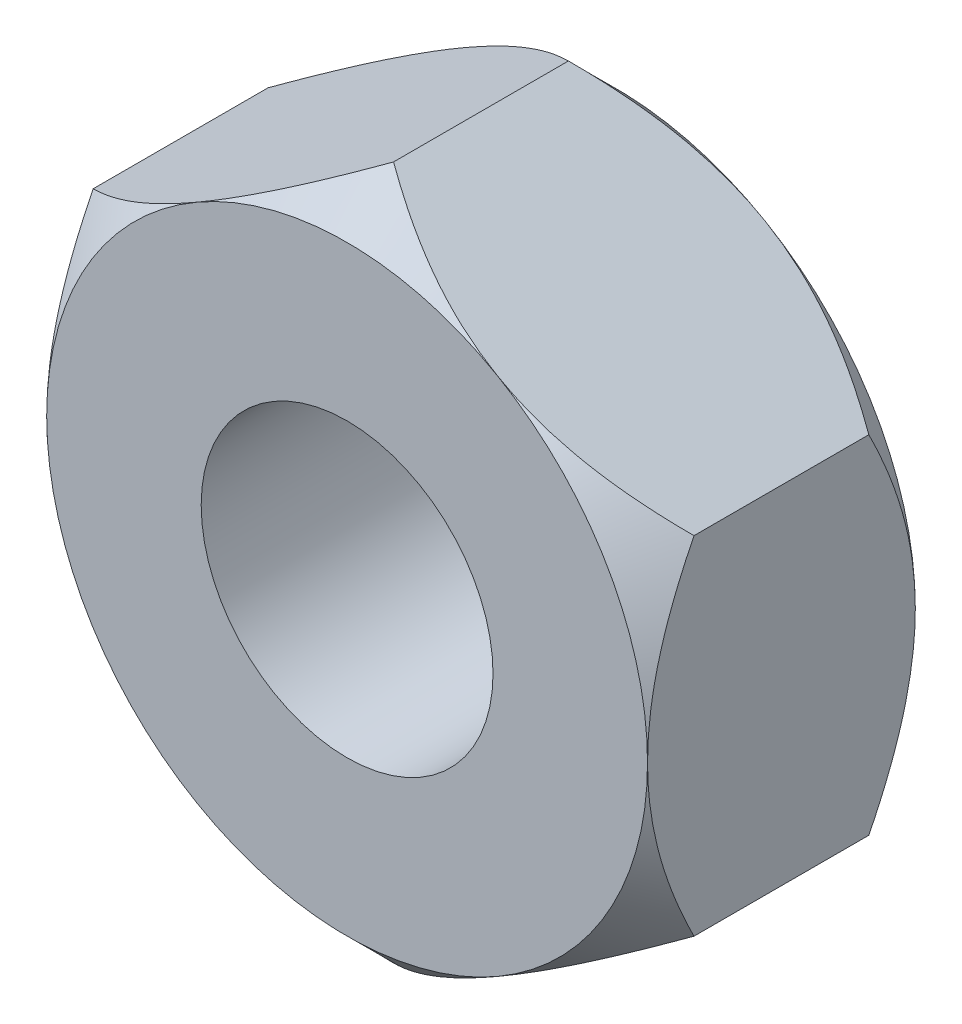
SolidWorks part; units mm, degrees
material "AISI 304"
ref_plane "前基準面" through (0, 0, 0) normal (0, 0, 1) x (1, 0, 0)
ref_plane "上基準面" through (0, 0, 0) normal (0, 1, 0) x (1, 0, 0)
ref_plane "右基準面" through (0, 0, 0) normal (1, 0, 0) x (0, 0, -1)
sketch "草圖4" plane through (0, 0, 0) normal (0, 1, 0) x (1, 0, 0)
  circle A0 centre (0, 0) radius 5
  dimension "D1" = 10
extrude "填料-伸長4" [suppressed] add sketch "草圖4" against normal blind 15
cosmetic thread "裝飾螺紋線1" [suppressed] parameters "D1"=8, "D2"=3
cosmetic thread "裝飾螺紋線2" [suppressed] parameters "D1"=15, "D2"=3
chamfer "導角2" [suppressed] distance 0.5 angle 45
sketch "草圖2" plane through (0, 0, 0) normal (0, 1, 0) x (1, 0, 0)
  circle A0 centre (0, 0) radius 3.5
  dimension "D1" = 7
extrude "填料-伸長2" [suppressed] add sketch "草圖2" along normal blind 3.5
sketch "草圖3" [suppressed] plane through (0, 2.8, 0) normal (0, 1, 0) x (1, 0, 0)
  line L0 (0, 1.7321) -> (0, 0) construction
  line L1 (0, 1.7321) -> (-1.5, 0.866)
  line L2 (-1.5, 0.866) -> (-1.5, -0.866)
  line L3 (-1.5, -0.866) -> (0, -1.7321)
  line L4 (0, -1.7321) -> (1.5, -0.866)
  line L5 (1.5, -0.866) -> (1.5, 0.866)
  line L6 (1.5, 0.866) -> (0, 1.7321)
  circle A0 centre (0, 0) radius 1.5 construction
  dimension "D1" = 3
extrude "除料-伸長1" [suppressed] cut sketch "草圖3" against normal blind 2
chamfer "導角1" [suppressed] distance 0.5 angle 45
sketch "草圖6" [suppressed] plane through (0, 0, 0) normal (0, 0, 1) x (1, 0, 0)
  line L0 (0, 0) -> (0, 2.3) construction
  line L1 (3.6593, 0) -> (0, 0)
  line L2 (0, 2.2) -> (1.9985, 2.2)
  line L3 (0, 0) -> (0, 2.2)
  arc A0 (2.0498, 2.1859) -> (3.7531, 0.1346) centre (0, -1.249) cw
  arc A1 (3.7531, 0.1346) -> (3.6593, 0) centre (3.6593, 0.1) cw
  arc A2 (2.0498, 2.1859) -> (1.9985, 2.2) centre (1.9985, 2.1) ccw
  point P7 (3.8, 0)
  point P12 (2.0259, 2.2)
  dimension "D3" = 0.1
  dimension "D5" = 4
  dimension "D6" = 0.1
  dimension "D1" = 7.6
  dimension "D2" = 2.3
  dimension "D4" = 2.2
revolve "旋轉1" [suppressed] add sketch "草圖6" angle 360 about L0
sketch "草圖7" [suppressed] plane through (0, 2.2, 0) normal (0, 1, 0) x (1, 0, 0)
  line L0 (0, 0) -> (0, 1.4434) construction
  line L1 (1.25, 0.7217) -> (0, 1.4434)
  line L2 (0, 1.4434) -> (-1.25, 0.7217)
  line L3 (-1.25, 0.7217) -> (-1.25, -0.7217)
  line L4 (-1.25, -0.7217) -> (0, -1.4434)
  line L5 (0, -1.4434) -> (1.25, -0.7217)
  line L6 (1.25, -0.7217) -> (1.25, 0.7217)
  circle A0 centre (0, 0) radius 1.25 construction
  dimension "D1" = 2.5
extrude "除料-伸長2" [suppressed] cut sketch "草圖7" against normal blind 1
chamfer "導角3" [suppressed] distance 0.5 angle 45
sketch "草圖8" [suppressed] plane through (0, 0, 0) normal (0, 1, 0) x (1, 0, 0)
  line L0 (0, 0) -> (0, 1.4434) construction
  line L1 (0, -1.4434) -> (1.25, -0.7217)
  line L2 (1.25, -0.7217) -> (1.25, 0.7217)
  line L3 (1.25, 0.7217) -> (0, 1.4434)
  line L4 (0, 1.4434) -> (-1.25, 0.7217)
  line L5 (-1.25, 0.7217) -> (-1.25, -0.7217)
  line L6 (-1.25, -0.7217) -> (0, -1.4434)
  circle A0 centre (0, 0) radius 1.25 construction
  dimension "D1" = 2.5
extrude "除料-伸長3" [suppressed] cut sketch "草圖8" against normal blind 2
sketch "草圖9" [suppressed] plane through (0, 0, 0) normal (0, 1, 0) x (1, 0, 0)
  line L0 (0, 0) -> (0, 7.5056) construction
  line L1 (0, 7.5056) -> (-6.5, 3.7528)
  line L2 (-6.5, 3.7528) -> (-6.5, -3.7528)
  line L3 (-6.5, -3.7528) -> (0, -7.5056)
  line L4 (0, -7.5056) -> (6.5, -3.7528)
  line L5 (6.5, -3.7528) -> (6.5, 3.7528)
  line L6 (6.5, 3.7528) -> (0, 7.5056)
  circle A0 centre (0, 0) radius 6.5 construction
  dimension "D1" = 13
extrude "填料-伸長5" [suppressed] add sketch "草圖9" along normal blind 5.5
sketch "草圖11" [suppressed] plane through (0, 5.5, 0) normal (0, 1, 0) x (1, 0, 0)
  line L0 (0, 0) -> (0, 13.0049) construction
sketch "草圖12" plane through (0, 0, 0) normal (0, 0, 1) x (1, 0, 0)
  line L0 (0, 0) -> (0, -8.0829) construction
  line L1 (7, -4.0415) -> (7, 4.0415)
  line L2 (7, 4.0415) -> (0, 8.0829)
  line L3 (0, 8.0829) -> (-7, 4.0415)
  line L4 (-7, 4.0415) -> (-7, -4.0415)
  line L5 (-7, -4.0415) -> (0, -8.0829)
  line L6 (0, -8.0829) -> (7, -4.0415)
  circle A0 centre (0, 0) radius 7 construction
  dimension "D1" = 14
extrude "填料-伸長6" add sketch "草圖12" along normal blind 6.24
hole_wizard "M8 螺紋孔2" positions "草圖15" profile "草圖14" tap size "M8" standard "ISO" end condition up to next
sketch "草圖15" plane through (0, 0, 0) normal (0, 0, -1) x (-1, 0, 0)
  point P0 (0, 0)
sketch "草圖14" plane through (0, 0, 0) normal (1, 0, 0) x (0, 1, 0)
  line L0 (0, 0) -> (0, 6.24)
  line L1 (0, 6.24) -> (3.4, 6.24)
  line L2 (3.4, 6.24) -> (3.4, 0)
  line L5 (3.4, 0) -> (0, 0)
  line L11 (0, -6.35) -> (0, 107.95) construction
  dimension "貫穿螺孔鑽直徑" = 6.8
  dimension "貫穿螺孔鑽深度" = 6.24
cosmetic thread "鑽孔螺紋3" parameters "D2"=8
sketch "草圖16" plane through (0, 0, 0) normal (0, 0, -1) x (-1, 0, 0)
  line L0 (-7, 4.0415) -> (0, 8.0829) construction
  circle A0 centre (0, 0) radius 7
sketch "草圖17" plane through (0, 0, 0) normal (1, 0, 0) x (0, 0, -1)
  line L0 (0, 8.0829) -> (-1.0829, 8.0829)
  line L1 (-6.24, 8.0829) -> (0, 8.0829) construction
  line L2 (-1.0829, 8.0829) -> (0, 7)
  line L3 (0, -7) -> (0, 7) construction
  line L4 (0, 7) -> (0, 8.0829)
  line L5 (-3.12, 8.0829) -> (-3.12, 0.2323) construction
  line L6 (-6.24, 7) -> (-6.24, 8.0829)
  line L7 (-5.1571, 8.0829) -> (-6.24, 7)
  line L8 (-6.24, 8.0829) -> (-5.1571, 8.0829)
revolve "除料-旋轉1" cut sketch "草圖17" angle 360 about axis through (0, 0, 0) along (0, 0, -1)
